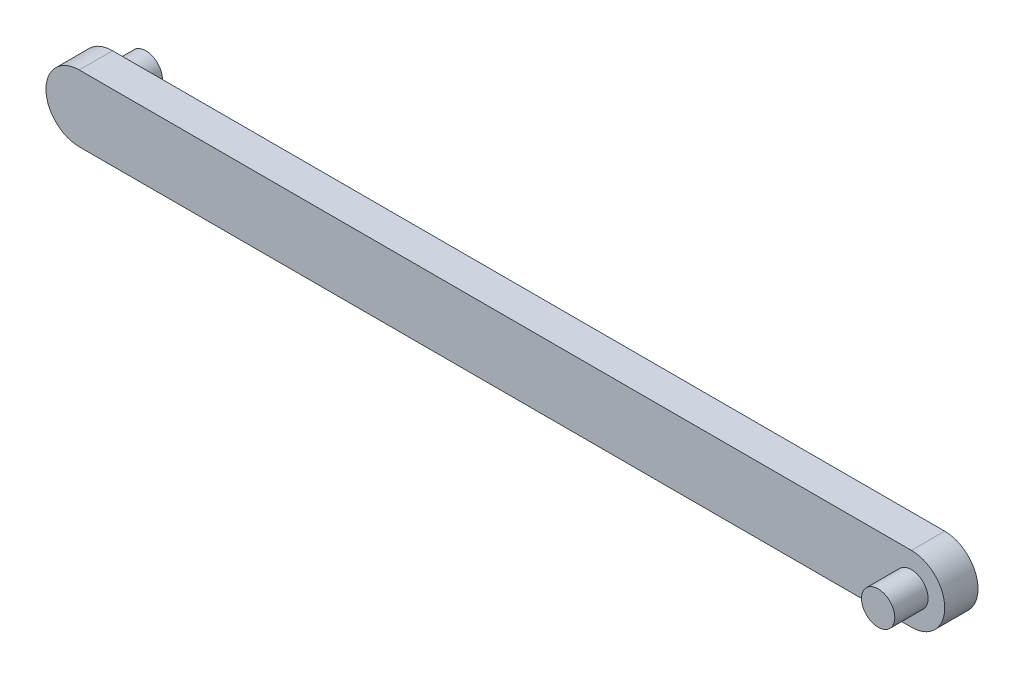
SolidWorks part; units mm, degrees
ref_plane "前视基准面" through (0, 0, 0) normal (0, 0, 1) x (1, 0, 0)
ref_plane "上视基准面" through (0, 0, 0) normal (0, 1, 0) x (1, 0, 0)
ref_plane "右视基准面" through (0, 0, 0) normal (1, 0, 0) x (0, 0, -1)
sketch "草图1" plane through (0, 0, 0) normal (0, 0, 1) x (1, 0, 0)
  line L1 (-16.3911, -2) -> (33.6089, -2)
  line L2 (-16.3911, 2) -> (33.6089, 2)
  arc A0 (33.6089, -2) -> (33.6089, 2) centre (33.6089, 0) ccw
  arc A1 (-16.3911, 2) -> (-16.3911, -2) centre (-16.3911, 0) ccw
  dimension "D1" = 50
extrude "凸台-拉伸1" add sketch "草图1" along normal blind 2
sketch "草图2" plane through (0, 0, 2) normal (0, 0, 1) x (1, 0, 0)
  circle A0 centre (33.6089, 0) radius 1
extrude "凸台-拉伸2" add sketch "草图2" along normal blind 2
sketch "草图3" plane through (0, 0, 0) normal (0, 0, -1) x (-1, 0, 0)
  circle A0 centre (16.3911, 0) radius 1
extrude "凸台-拉伸3" add sketch "草图3" along normal blind 2
